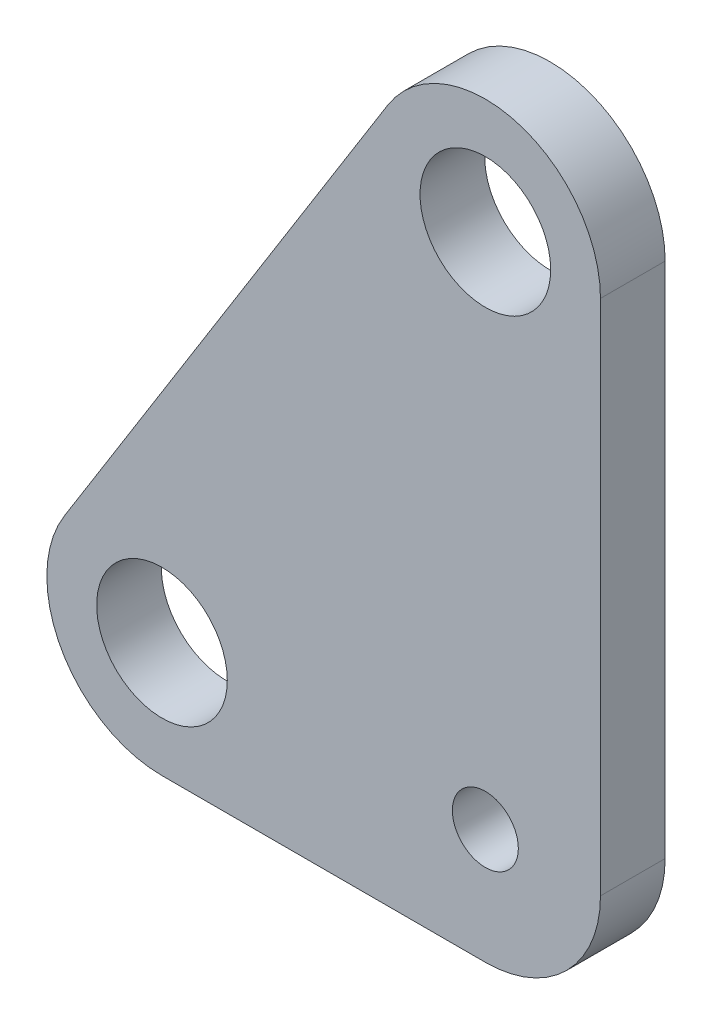
SolidWorks part; units mm, degrees
material "ABS"
ref_plane "Plan de face" through (0, 0, 0) normal (0, 0, 1) x (1, 0, 0)
ref_plane "Plan de dessus" through (0, 0, 0) normal (0, 1, 0) x (1, 0, 0)
ref_plane "Plan de droite" through (0, 0, 0) normal (1, 0, 0) x (0, 0, -1)
sketch "Esquisse2" plane through (0, 0, 0) normal (0, 0, 1) x (1, 0, 0)
  line L3 (-41.3349, 5.9906) -> (-9.5849, 56.7906)
  line L4 (-31.75, -11.303) -> (0, -11.303)
  line L5 (11.303, 0) -> (11.303, 50.8)
  arc A6 (0, -11.303) -> (11.303, 0) centre (0, 0) ccw
  circle A7 centre (0, 0) radius 3.2385
  circle A8 centre (-31.75, 0) radius 6.4135
  arc A9 (-41.3349, 5.9906) -> (-31.75, -11.303) centre (-31.75, 0) ccw
  circle A10 centre (0, 50.8) radius 6.4135
  arc A11 (11.303, 50.8) -> (-9.5849, 56.7906) centre (0, 50.8) ccw
  dimension "D3" = 31.75
  dimension "D4" = 50.8
  dimension "D1" = 12.827
  dimension "D2" = 11.303
  dimension "D5" = 6.477
extrude "Boss.-Extru.1" add sketch "Esquisse2" along normal blind 6.35
